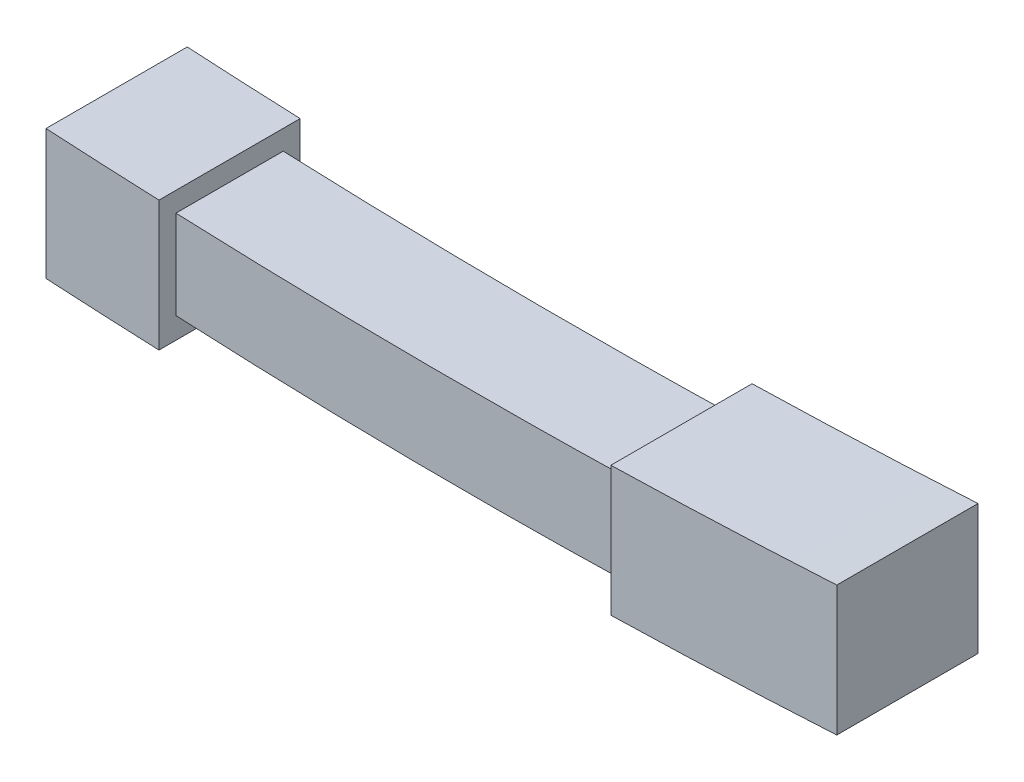
SolidWorks part; units mm, degrees
ref_plane "Front Plane" through (0, 0, 0) normal (0, 0, 1) x (1, 0, 0)
ref_plane "Top Plane" through (0, 0, 0) normal (0, 1, 0) x (1, 0, 0)
ref_plane "Right Plane" through (0, 0, 0) normal (1, 0, 0) x (0, 0, -1)
sketch "Sketch1" plane through (0, 0, 0) normal (0, 1, 0) x (1, 0, 0)
  line L1 (70, -12.5) -> (-70, -12.5)
  line L2 (70, -12.5) -> (70, 12.5)
  line L3 (70, 12.5) -> (-70, 12.5)
  line L4 (-70, -12.5) -> (-70, 12.5)
  line L5 (70, -12.5) -> (-70, 12.5) construction
  line L6 (70, 12.5) -> (-70, -12.5) construction
  point P0 (0, 0)
  point P5 (-70, 0)
  dimension "D1" = 140
  dimension "D2" = 25
extrude "Boss-Extrude1" add sketch "Sketch1" along normal blind 25
sketch "Sketch2" plane through (0, 0, 12.5) normal (0, 0, 1) x (1, 0, 0)
  line L0 (-70, 22.8376) -> (70, 22.8376)
  line L1 (-70, 25) -> (-70, 0) construction
  line L2 (70, 25) -> (70, 0) construction
  spline S0 degree 2 poles (-70, 12.5) (0, 10.0003) (70, 12.5) knots 0 0 0 1 1 1
  point P8 (-500000, 60752.5992)
sketch "Sketch3" plane through (-70, 0, 0) normal (-1, 0, 0) x (0, 0, 1)
  line L0 (12.5, 25) -> (-12.5, 0)
  line L1 (-12.5, 25) -> (12.5, 0)
  circle A0 centre (0, 12.5) radius 12.5
  point P10 (14.9425, 56.9827)
sketch "Sketch4" plane through (70, 0, 0) normal (1, 0, 0) x (0, 0, -1)
  line L0 (12.5, 25) -> (-12.5, 0)
  line L1 (-12.5, 25) -> (12.5, 0)
  circle A0 centre (0, 12.5) radius 12.4007
  point P10 (-7.4057, 0.9787)
sketch "Sketch5" plane through (0, 0, 12.5) normal (0, 0, 1) x (1, 0, 0)
  line L0 (30, 23.3673) -> (30, 19.8673)
  line L1 (-70, 25) -> (70, 25)
  line L2 (-50, 24.0204) -> (-50, 20.5204)
  line L3 (-70, 25) -> (70, 25) construction
  line L4 (-50, 20.5204) -> (-50, 1.0204)
  line L5 (30, 25) -> (-50, 25)
  line L6 (0, 11.2502) -> (0, 25)
  line L7 (-70, 21.5) -> (-50, 21.5)
  line L8 (0, 11.2502) -> (0, 14.7502)
  line L9 (-70, 25) -> (-70, 21.5)
  line L10 (-50, 1.0204) -> (-50, 4.813)
  line L11 (-70, 0) -> (-70, 2)
  line L12 (-70, 2) -> (-70, 0)
  line L13 (-70, 0) -> (70, 0)
  line L14 (70, 0) -> (70, 2)
  line L15 (0, 23) -> (0, 19.5)
  line L16 (30, 23.3673) -> (30, 0.3673)
  line L17 (30, 0.3673) -> (30, 3.8673)
  line L18 (0, 0) -> (0, 3.5)
  spline S0 degree 2 poles (-70, 25) (0, 21) (70, 25) knots 0 0 0 1 1 1
  spline S1 degree 2 poles (-70, 2) (0, -2) (70, 2) knots 0 0 0 1 1 1
  spline S2 degree 2 poles (-50, 20.5204) (-10.0053, 18.8878) (30, 19.8673) knots 0 0 0 1 1 1
  spline S3 degree 2 poles (-50, 4.813) (-10.0108, 2.8) (30, 3.8673) knots 0 0 0 1 1 1
  point P34 (0, 0)
  line M4 (-70, 0) -> (70, 0)
  line M5 (70, 0) -> (70, 25)
  line M6 (70, 25) -> (-70, 25)
  line M7 (-70, 25) -> (-70, 0)
  dimension "D1" = 3.5
  dimension "D2" = 3.5
  dimension "D3" = 3.5
  dimension "D4" = 3.5
  dimension "D5" = 3.5
  dimension "D6" = 3.5
  dimension "D7" = 3.5
  dimension "D8" = 3.5
extrude "Cut-Extrude1" cut sketch "Sketch5" against normal blind 25 contours S0 L6 L5 M6 | L6 S0 L1 M6 | L6 S2 L0 S0 | L2 S2 L6 S0 | S3 L4 S1 L18 | S3 L18 S1 L16 | S1 L13 M5 | S1 M7 M4
sketch "Sketch6" plane through (0, 0, 12.5) normal (0, 0, 1) x (1, 0, 0)
  line L0 (30, 19.8673) -> (30, 3.8673)
  line L1 (-50, 20.5204) -> (-50, 4.813)
  line L2 (30, 3.8673) -> (30, 1.4859)
  line L3 (30, 1.4859) -> (-50, 1.4859)
  line L4 (-50, 4.813) -> (-50, 1.0204) construction
  line L5 (-50, 1.4859) -> (-50, 4.813)
  line L6 (-50, 20.5204) -> (30, 19.8673)
  line L7 (-50, 20.5204) -> (-50, 21.4699)
  line L8 (-50, 24.0204) -> (-50, 20.5204) construction
  line L10 (30, 23.3673) -> (30, 19.8673) construction
  line L11 (30, 20.9952) -> (30, 19.8673)
  line L13 (-50, 21.4699) -> (30, 21.4699)
  line L14 (-50, 21.4699) -> (-50, 1.4859)
  line L15 (-50, 1.4859) -> (30, 1.4859)
  line L16 (30, 21.4699) -> (30, 1.4859)
  line M8 (30, 23.3673) -> (30, 19.8673)
  spline M9 degree 2 poles (30, 19.8673) (-10.0053, 18.8878) (-50, 20.5204) knots 0 0 0 1 1 1
  line M10 (-50, 20.5204) -> (-50, 24.0204)
  line M14 (-50, 1.0204) -> (-50, 4.813)
  spline M15 degree 2 poles (-50, 4.813) (-10.0108, 2.8) (30, 3.8673) knots 0 0 0 1 1 1
  line M16 (30, 3.8673) -> (30, 0.3673)
extrude "Cut-Extrude13" cut sketch "Sketch6" against normal blind 3 contours L3 M16 M15 M14 | L1 L0 M9 M15 | L13 L6 M10 M8 | L6 M9
sketch "Sketch9" plane through (0, 0, -12.5) normal (0, 0, -1) x (-1, 0, 0)
  line L0 (-30, 23.3673) -> (-30, 19.8673) construction
  line L1 (-30, 21.6173) -> (50, 21.6173)
  line L2 (-30, 21.6173) -> (-30, 2.9167)
  line L3 (-30, 2.9167) -> (50, 2.9167)
  line L4 (50, 21.6173) -> (50, 2.9167)
  line L5 (50, 4.813) -> (50, 1.0204) construction
extrude "Cut-Extrude14" cut sketch "Sketch9" against normal blind 3
